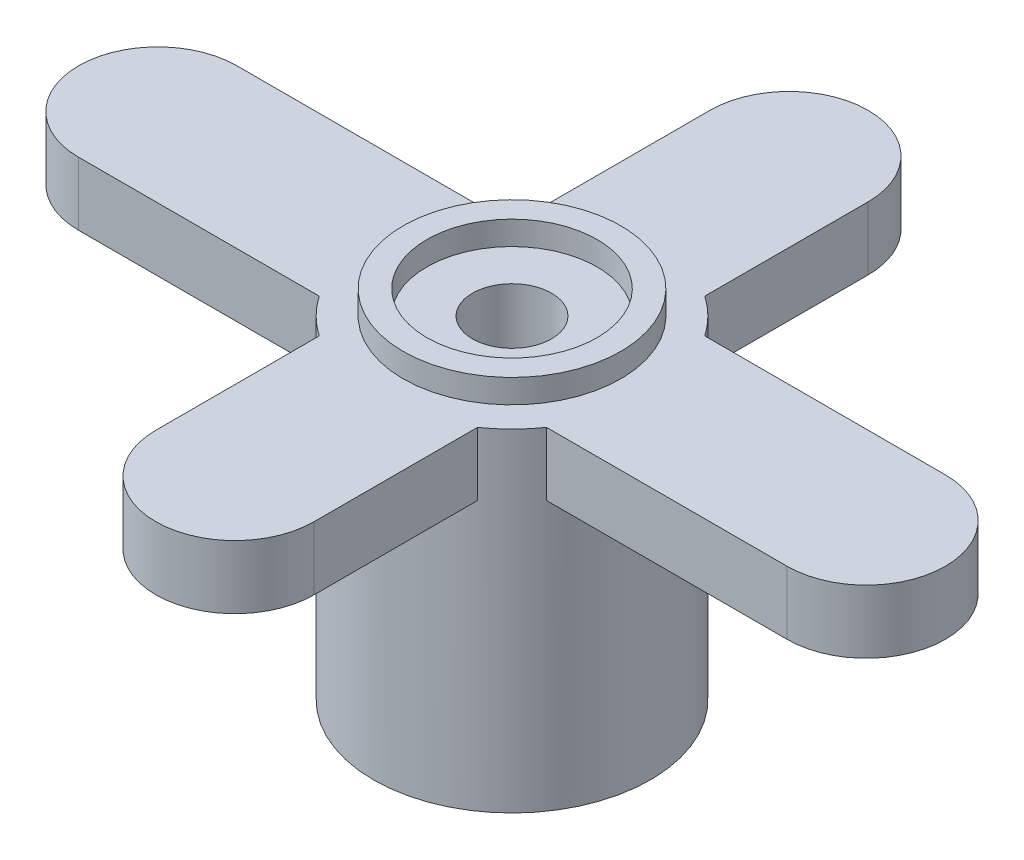
SolidWorks part; units mm, degrees
ref_plane "Płaszczyzna przednia" through (0, 0, 0) normal (0, 0, 1) x (1, 0, 0)
ref_plane "Płaszczyzna górna" through (0, 0, 0) normal (0, 1, 0) x (1, 0, 0)
ref_plane "Płaszczyzna prawa" through (0, 0, 0) normal (1, 0, 0) x (0, 0, -1)
sketch "Szkic1" plane through (0, 0, 0) normal (0, 1, 0) x (1, 0, 0)
  circle A0 centre (0, 0) radius 3.5
  dimension "D1" = 7
extrude "Dodanie-wyciągnięcie1" add sketch "Szkic1" along normal blind 9
sketch "Szkic2" plane through (0, 0, 0) normal (0, -1, 0) x (1, 0, 0)
  circle A0 centre (0, 0) radius 1.9
  dimension "D1" = 3.8
extrude "Wytnij-wyciągnięcie1" cut sketch "Szkic2" against normal blind 3.5
ref_plane "Płaszczyzna1" through (0, 8.4, 0) normal (0, 1, 0) x (1, 0, 0)
sketch "Szkic3" plane through (0, 8.4, 0) normal (0, 1, 0) x (1, 0, 0)
  line L0 (0, 0) -> (15.3312, 0) construction
  line L1 (0, 0) -> (0, 11.7192) construction
  line L2 (-8.95, 2) -> (0, 2)
  line L3 (0, 2) -> (8.95, 2)
  line L4 (-8.95, -2) -> (8.95, -2)
  line L5 (-2, -7) -> (-2, 7)
  line L6 (2, -7) -> (2, 0)
  line L7 (2, 0) -> (2, 7)
  circle A0 centre (8.95, 0) radius 2
  circle A1 centre (-8.95, 0) radius 2
  circle A2 centre (0, 7) radius 2
  circle A3 centre (0, -7) radius 2
  dimension "D1" = 4
  dimension "D2" = 4
  dimension "D4" = 4
  dimension "D5" = 4
  dimension "D3" = 17.9
  dimension "D6" = 14
extrude "Dodanie-wyciągnięcie2" add sketch "Szkic3" against normal blind 1.6 contours A1 | A1 L4 L5 L2 | A2 | A2 L5 L2 L3 L7 | A0 L3 L7 L6 L4 | A0 | A3 | A3 L6 L4 L5
sketch "Szkic4" plane through (0, 9, 0) normal (0, 1, 0) x (1, 0, 0)
  circle A0 centre (0, 0) radius 2.15
  dimension "D1" = 4.3
extrude "Wytnij-wyciągnięcie2" cut sketch "Szkic4" against normal up to surface (0.6 mm away)
sketch "Szkic5" plane through (0, 8.4, 0) normal (0, 1, 0) x (1, 0, 0)
  circle A0 centre (0, 0) radius 1
  dimension "D1" = 2
extrude "Wytnij-wyciągnięcie3" cut sketch "Szkic5" against normal blind 31.6
sketch "Szkic6" plane through (0, 9, 0) normal (0, 1, 0) x (1, 0, 0)
  circle A0 centre (0, 0) radius 3.5 construction
  circle A1 centre (0, 0) radius 2.75
  circle A2 centre (0, 0) radius 3.5
  dimension "D1" = 5.5
extrude "Wytnij-wyciągnięcie4" cut sketch "Szkic6" against normal up to surface (0.6 mm away) up to face at (-6.5681, 8.4, 0)
